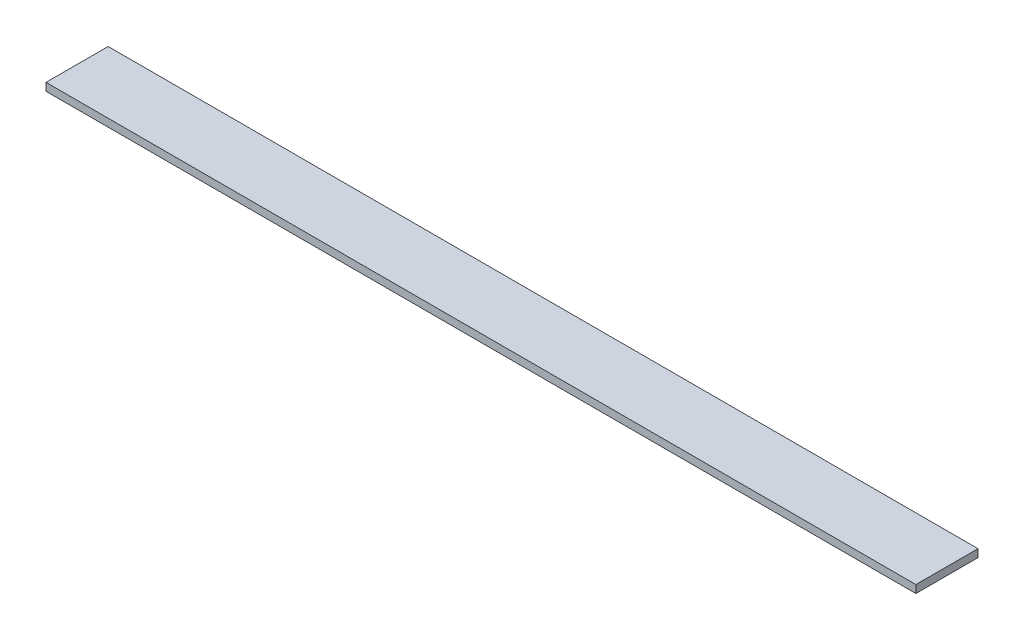
SolidWorks part; units mm, degrees
ref_plane "Front Plane" through (0, 0, 0) normal (0, 0, 1) x (1, 0, 0)
ref_plane "Top Plane" through (0, 0, 0) normal (0, 1, 0) x (1, 0, 0)
ref_plane "Right Plane" through (0, 0, 0) normal (1, 0, 0) x (0, 0, -1)
sketch "Sketch1" plane through (0, 0, 0) normal (0, 1, 0) x (1, 0, 0)
  line L1 (-51.0353, 21.6514) -> (304.5647, 21.6514)
  line L2 (-51.0353, 21.6514) -> (-51.0353, -3.7486)
  line L3 (-51.0353, -3.7486) -> (304.5647, -3.7486)
  line L4 (304.5647, 21.6514) -> (304.5647, -3.7486)
  dimension "D1" = 355.6
  dimension "D2" = 25.4
extrude "Boss-Extrude1" add sketch "Sketch1" along normal blind 3.175 contours L1 L4 L3 L2
